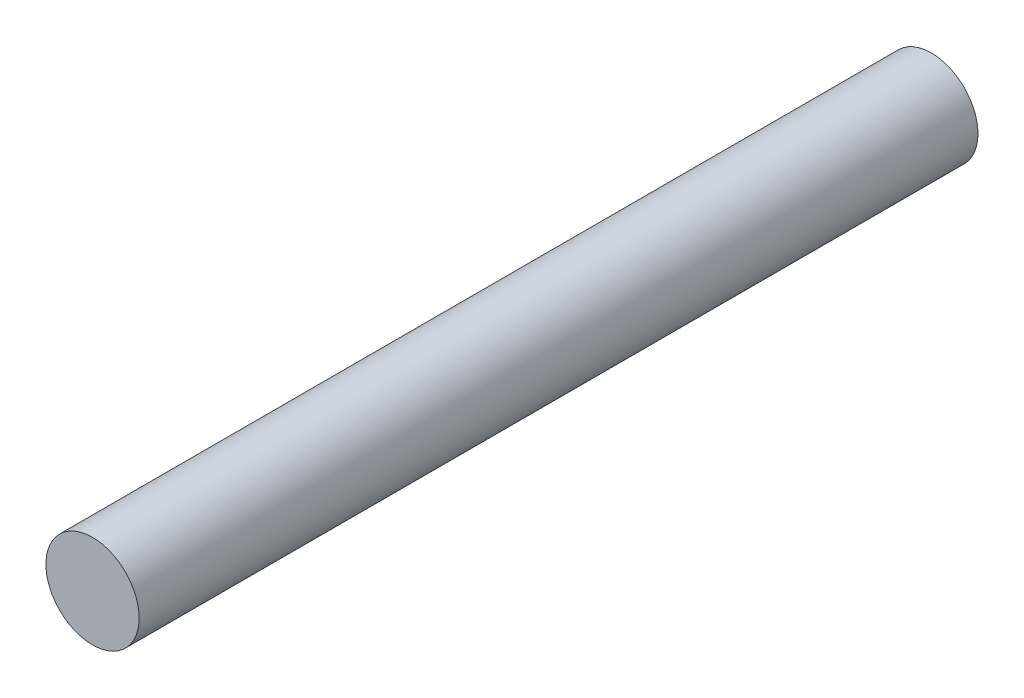
SolidWorks part; units mm, degrees
ref_plane "Front Plane" through (0, 0, 0) normal (0, 0, 1) x (1, 0, 0)
ref_plane "Top Plane" through (0, 0, 0) normal (0, 1, 0) x (1, 0, 0)
ref_plane "Right Plane" through (0, 0, 0) normal (1, 0, 0) x (0, 0, -1)
sketch "Sketch1" plane through (0, 0, 0) normal (0, 0, 1) x (1, 0, 0)
  circle A0 centre (0, 0) radius 2.5
  dimension "D1" = 5
extrude "Boss-Extrude1" add sketch "Sketch1" along normal blind 45
